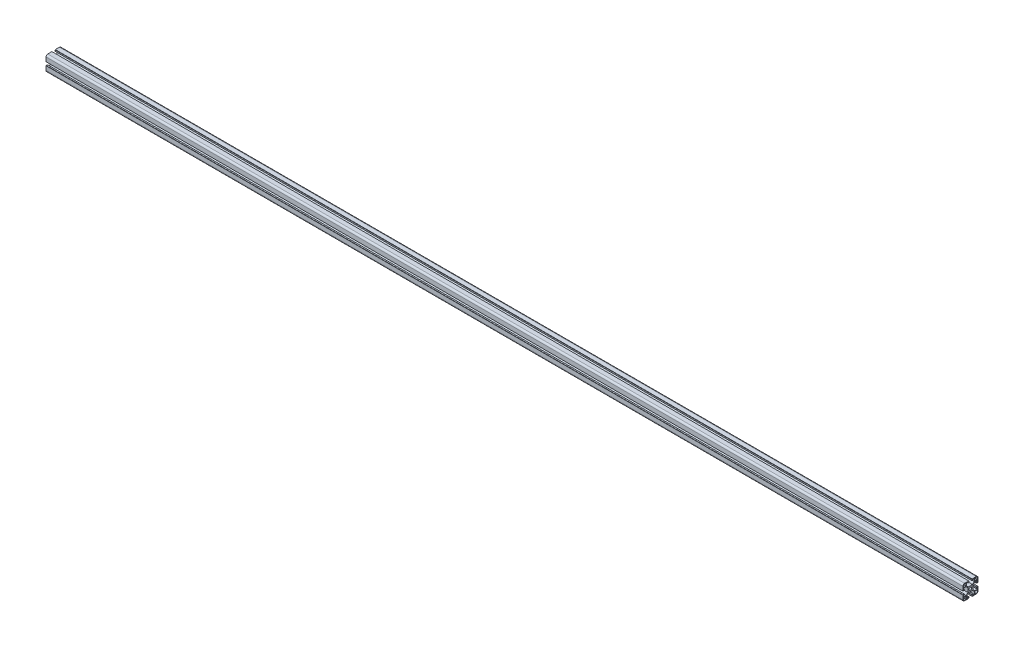
SolidWorks part; units mm, degrees
ref_plane "前视基准面" through (0, 0, 0) normal (0, 0, 1) x (1, 0, 0)
ref_plane "上视基准面" through (0, 0, 0) normal (0, 1, 0) x (1, 0, 0)
ref_plane "右视基准面" through (0, 0, 0) normal (1, 0, 0) x (0, 0, -1)
sketch "草图3" plane through (0, 0, 0) normal (1, 0, 0) x (0, 0, -1)
  line L1 (-15.5, -20) -> (-4.5, -20)
  line L2 (-20, -15.5) -> (-20, -4.5)
  line L3 (-15.5, 20) -> (-4.5, 20)
  line L4 (20, -15.5) -> (20, -4.5)
  line L8 (-20, 4.5) -> (-19.5, 4.5)
  line L9 (-19.5, 4.5) -> (-19.5, 4.1)
  line L10 (-19.5, 4.1) -> (-16.2, 4.1)
  line L11 (-16.2, 4.1) -> (-16.2, 6.4)
  line L12 (-16.2, 6.4) -> (-18.2, 6.4)
  line L13 (-18.2, 6.4) -> (-18.2, 10.25)
  line L14 (-18.2, 10.25) -> (-11.5228, 10.25)
  line L15 (-11.5228, 10.25) -> (-6.7519, 5.4791)
  line L16 (-6.7519, 5.4791) -> (-6.7519, -5.4791)
  line L21 (6.7519, 5.4791) -> (6.7519, -5.4791)
  line L22 (11.5228, 10.25) -> (6.7519, 5.4791)
  line L23 (18.2, 10.25) -> (11.5228, 10.25)
  line L24 (18.2, 6.4) -> (18.2, 10.25)
  line L25 (16.2, 6.4) -> (18.2, 6.4)
  line L26 (16.2, 4.1) -> (16.2, 6.4)
  line L27 (19.5, 4.1) -> (16.2, 4.1)
  line L28 (19.5, 4.5) -> (19.5, 4.1)
  line L29 (20, 4.5) -> (19.5, 4.5)
  line L30 (20, -4.5) -> (19.5, -4.5)
  line L31 (19.5, -4.5) -> (19.5, -4.1)
  line L32 (19.5, -4.1) -> (16.2, -4.1)
  line L33 (16.2, -4.1) -> (16.2, -6.4)
  line L34 (16.2, -6.4) -> (18.2, -6.4)
  line L35 (18.2, -6.4) -> (18.2, -10.25)
  line L36 (18.2, -10.25) -> (11.5228, -10.25)
  line L37 (11.5228, -10.25) -> (6.7519, -5.4791)
  line L38 (-11.5228, -10.25) -> (-6.7519, -5.4791)
  line L39 (-18.2, -10.25) -> (-11.5228, -10.25)
  line L40 (-18.2, -6.4) -> (-18.2, -10.25)
  line L41 (-16.2, -6.4) -> (-18.2, -6.4)
  line L42 (-16.2, -4.1) -> (-16.2, -6.4)
  line L43 (-19.5, -4.1) -> (-16.2, -4.1)
  line L44 (-19.5, -4.5) -> (-19.5, -4.1)
  line L45 (-20, -4.5) -> (-19.5, -4.5)
  line L46 (-4.5, -20) -> (-4.5, -19.5)
  line L47 (-4.5, -19.5) -> (-4.1, -19.5)
  line L48 (-4.1, -19.5) -> (-4.1, -16.2)
  line L49 (-4.1, -16.2) -> (-6.4, -16.2)
  line L50 (-6.4, -16.2) -> (-6.4, -18.2)
  line L51 (-6.4, -18.2) -> (-10.25, -18.2)
  line L52 (-10.25, -18.2) -> (-10.25, -11.5228)
  line L53 (-10.25, -11.5228) -> (-5.4791, -6.7519)
  line L56 (5.4791, -6.7519) -> (-5.4791, -6.7519)
  line L57 (10.25, -11.5228) -> (5.4791, -6.7519)
  line L58 (10.25, -18.2) -> (10.25, -11.5228)
  line L59 (6.4, -18.2) -> (10.25, -18.2)
  line L60 (6.4, -16.2) -> (6.4, -18.2)
  line L61 (4.1, -16.2) -> (6.4, -16.2)
  line L62 (4.1, -19.5) -> (4.1, -16.2)
  line L63 (4.5, -19.5) -> (4.1, -19.5)
  line L64 (4.5, -20) -> (4.5, -19.5)
  line L65 (-10.25, 11.5228) -> (-5.4791, 6.7519)
  line L66 (-10.25, 18.2) -> (-10.25, 11.5228)
  line L67 (-6.4, 18.2) -> (-10.25, 18.2)
  line L68 (-6.4, 16.2) -> (-6.4, 18.2)
  line L69 (-4.1, 16.2) -> (-6.4, 16.2)
  line L70 (-4.1, 19.5) -> (-4.1, 16.2)
  line L71 (-4.5, 19.5) -> (-4.1, 19.5)
  line L72 (-4.5, 20) -> (-4.5, 19.5)
  line L73 (4.5, 20) -> (4.5, 19.5)
  line L74 (4.5, 19.5) -> (4.1, 19.5)
  line L75 (4.1, 19.5) -> (4.1, 16.2)
  line L76 (4.1, 16.2) -> (6.4, 16.2)
  line L77 (6.4, 16.2) -> (6.4, 18.2)
  line L78 (6.4, 18.2) -> (10.25, 18.2)
  line L79 (10.25, 18.2) -> (10.25, 11.5228)
  line L80 (10.25, 11.5228) -> (5.4791, 6.7519)
  line L81 (5.4791, 6.7519) -> (-5.4791, 6.7519)
  line L82 (20, 4.5) -> (20, 15.5)
  line L84 (4.5, 20) -> (15.5, 20)
  line L85 (-20, 4.5) -> (-20, 15.5)
  line L86 (4.5, -20) -> (15.5, -20)
  arc A0 (-15.5, -20) -> (-20, -15.5) centre (-15.5, -15.5) cw
  arc A1 (15.5, -20) -> (20, -15.5) centre (15.5, -15.5) ccw
  arc A2 (15.5, 20) -> (20, 15.5) centre (15.5, 15.5) cw
  arc A3 (-20, 15.5) -> (-15.5, 20) centre (-15.5, 15.5) cw
  circle A4 centre (0, 0) radius 3.4
  point P0 (0, 0)
  dimension "D3" = 4.5
  dimension "D4" = 6.8
  dimension "D7" = 1.8
  dimension "D10" = 0.5
  dimension "D11" = 13.2481
  dimension "D13" = 2
extrude "凸台-拉伸1" add sketch "草图3" along normal blind 2421
ref_plane "基准面1" through (2421, -20, 15.5) normal (-1, 0, 0) x (0, 0, 1)
sketch "草图4" plane through (2421, -20, 15.5) normal (-1, 0, 0) x (0, 0, 1)
  line L0 (-5.25, 31.5228) -> (-5.25, 38.2) construction
  line L1 (-3.75, 31.75) -> (3, 31.75)
  line L2 (-3.75, 31.75) -> (-3.75, 38.5)
  line L3 (-3.75, 38.5) -> (0, 38.5)
  line L4 (3, 31.75) -> (3, 35.5)
  line L5 (4.5, 35.5) -> (4.5, 24.5) construction
  line L6 (-11, 40) -> (0, 40) construction
  line L7 (2.7, 30.25) -> (-3.9772, 30.25) construction
  line L8 (-3.75, 8.25) -> (-3.75, 1.5)
  line L9 (-3.75, 8.25) -> (3, 8.25)
  line L10 (3, 8.25) -> (3, 4.5)
  line L11 (-3.75, 1.5) -> (0, 1.5)
  line L12 (-27.25, 8.25) -> (-34, 8.25)
  line L13 (-27.25, 8.25) -> (-27.25, 1.5)
  line L14 (-27.25, 1.5) -> (-31, 1.5)
  line L15 (-34, 8.25) -> (-34, 4.5)
  line L16 (-27.25, 31.75) -> (-27.25, 38.5)
  line L17 (-27.25, 31.75) -> (-34, 31.75)
  line L18 (-34, 31.75) -> (-34, 35.5)
  line L19 (-27.25, 38.5) -> (-31, 38.5)
  arc A0 (0, 38.5) -> (3, 35.5) centre (0, 35.5) cw
  arc A1 (3, 4.5) -> (0, 1.5) centre (0, 4.5) cw
  arc A2 (-31, 1.5) -> (-34, 4.5) centre (-31, 4.5) cw
  arc A3 (-34, 35.5) -> (-31, 38.5) centre (-31, 35.5) cw
  dimension "D5" = 3
  dimension "D1" = 1.5
  dimension "D2" = 1.5
  dimension "D3" = 1.5
  dimension "D4" = 1.5
  dimension "D6" = 4
extrude "切除-拉伸3" cut sketch "草图4" along normal blind 3297
